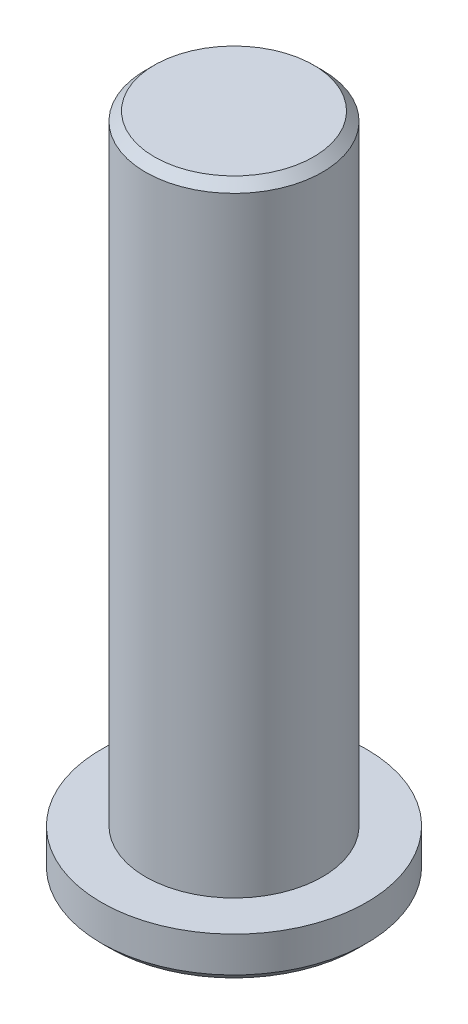
SolidWorks part; units mm, degrees
material "AISI 1045 钢，冷拔"
ref_plane "前视基准面" through (0, 0, 0) normal (0, 0, 1) x (1, 0, 0)
ref_plane "上视基准面" through (0, 0, 0) normal (0, 1, 0) x (1, 0, 0)
ref_plane "右视基准面" through (0, 0, 0) normal (1, 0, 0) x (0, 0, -1)
sketch "草图1" plane through (0, 0, 0) normal (0, 1, 0) x (1, 0, 0)
  circle A0 centre (0, 0) radius 15
  dimension "D1" = 30
extrude "凸台-拉伸1" add sketch "草图1" along normal blind 5
sketch "草图2" plane through (0, 5, 0) normal (0, 1, 0) x (1, 0, 0)
  circle A0 centre (0, 0) radius 10
  dimension "D1" = 20
extrude "凸台-拉伸2" add sketch "草图2" along normal blind 70
chamfer "倒角1" distance 1 angle 45 2 edges at (0, 75, 10) (0, 0, 15)
